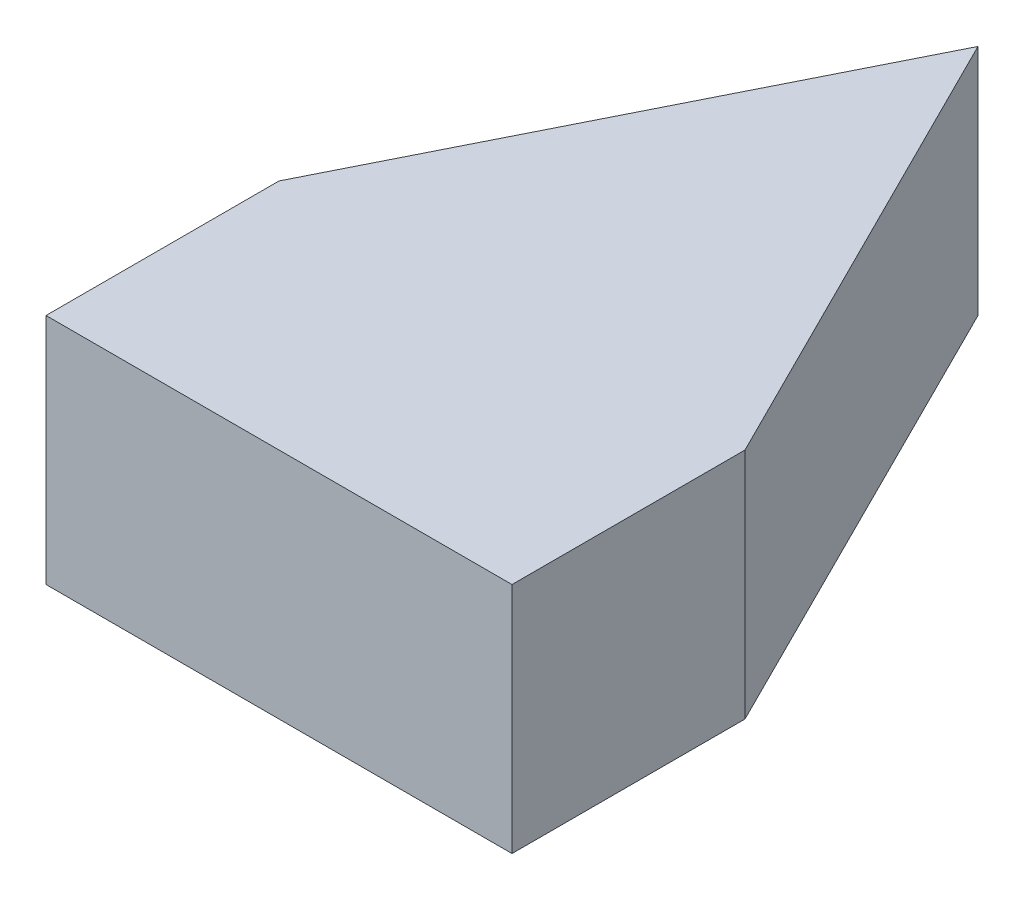
SolidWorks part; units mm, degrees
ref_plane "Front" through (0, 0, 0) normal (0, 0, 1) x (1, 0, 0)
ref_plane "Top" through (0, 0, 0) normal (0, 1, 0) x (1, 0, 0)
ref_plane "Right" through (0, 0, 0) normal (1, 0, 0) x (0, 0, -1)
sketch "Needle Point Sketch" plane through (0, 0, 0) normal (0, 1, 0) x (1, 0, 0)
  line L0 (0, 0) -> (6.35, 0) construction
  line L1 (6.35, 0) -> (3.175, 6.35)
  line L2 (3.175, 6.35) -> (0, 0)
  line L3 (3.175, 6.35) -> (3.175, 0) construction
  line L5 (0, 0) -> (6.35, 0) construction
  line L6 (0, 0) -> (0, -3.175)
  line L7 (0, -3.175) -> (6.35, -3.175)
  line L8 (6.35, 0) -> (6.35, -3.175)
  point P7 (0, 0)
  dimension "D1" = 6.35
  dimension "D2" = 6.35
  dimension "D3" = 3.175
extrude "Needle Point" add sketch "Needle Point Sketch" along normal blind 3.175
